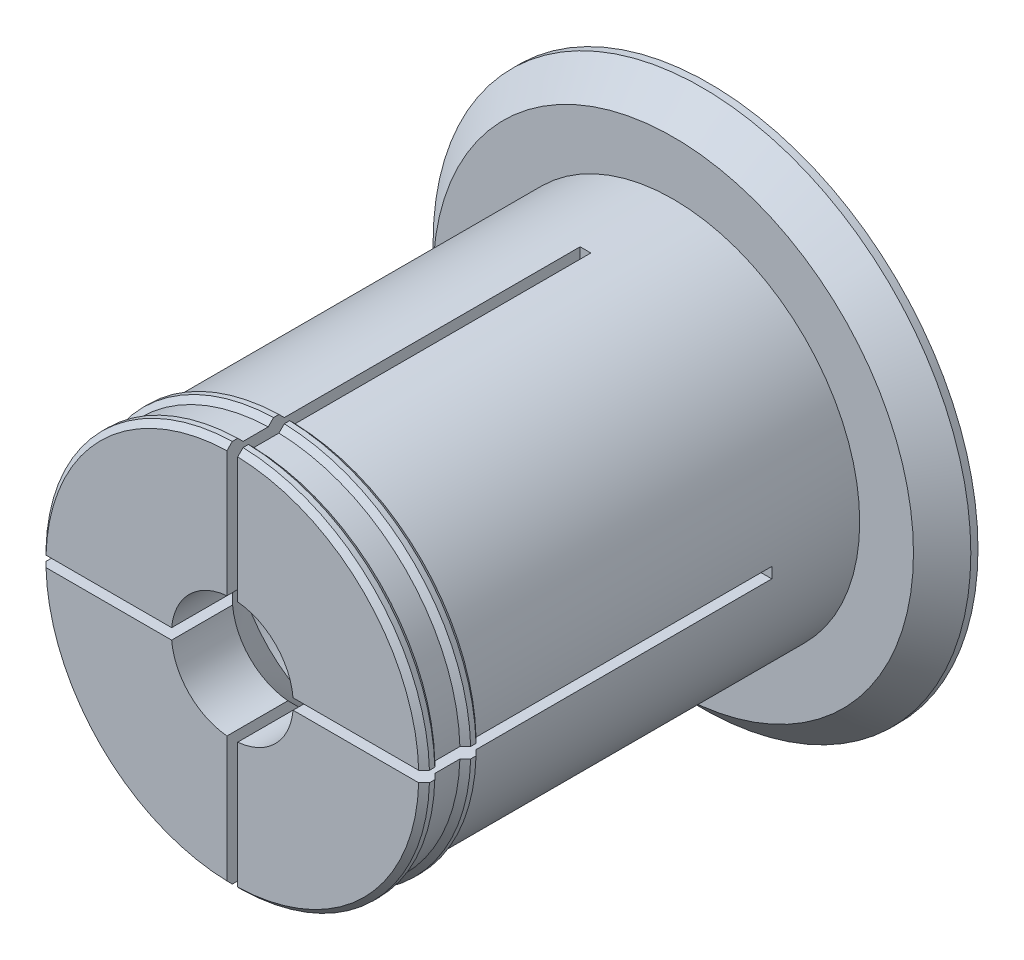
SolidWorks part; units mm, degrees
ref_plane "Front" through (0, 0, 0) normal (0, 0, 1) x (1, 0, 0)
ref_plane "Top" through (0, 0, 0) normal (0, 1, 0) x (1, 0, 0)
ref_plane "Right" through (0, 0, 0) normal (1, 0, 0) x (0, 0, -1)
sketch "Axle base sketch" plane through (0, 0, 0) normal (0, 0, 1) x (1, 0, 0)
  circle A0 centre (0, 0) radius 26
  dimension "D1" = 52
extrude "Axle" add sketch "Axle base sketch" along normal blind 61.5
sketch "Guard base" plane through (0, 0, 0) normal (0, 0, -1) x (-1, 0, 0)
  circle A0 centre (0, 0) radius 37.5
  dimension "D1" = 75
extrude "Guard" add sketch "Guard base" along normal blind 5
sketch "Inner axle hole base" plane through (0, 0, 61.5) normal (0, 0, 1) x (1, 0, 0)
  circle A0 centre (0, 0) radius 8.5
  dimension "D1" = 17
extrude "Inner axle hole" cut sketch "Inner axle hole base" against normal through all
sketch "Mate ring base" plane through (0, 0, 0) normal (0, 1, 0) x (1, 0, 0)
  line L0 (26, -61.5) -> (26.75, -60.75)
  line L1 (26.75, -60.75) -> (26.75, -60)
  line L2 (26.75, -60) -> (26, -59.25)
  line L3 (26.75, -60.75) -> (26.75, -61.5) construction
  line L4 (26.75, -61.5) -> (26, -61.5) construction
  line L5 (26, -59.25) -> (26, -61.5)
  line L6 (26, -61.5) -> (26, 0) construction
  line L8 (26, -55.75) -> (26.75, -55)
  line L9 (26.75, -55) -> (26.75, -54.25)
  line L10 (26.75, -54.25) -> (26, -53.5)
  line L11 (26, -53.5) -> (26, -55.75)
  dimension "D1" = 0.75
  dimension "D2" = 0.75
  dimension "D3" = 5
  dimension "D4" = 0.75
ref_axis "Center Z" through (0, 0, 0) along (0, 0, -1)
revolve "Mate rings" add sketch "Mate ring base" angle 360 about axis through (0, 0, 0) along (0, 0, -1)
sketch "Inner mass remove base" plane through (0, 0, 0) normal (1, 0, 0) x (0, 0, -1)
  line L0 (-61.5, 0) -> (-44.25, -17.25)
  line L1 (-44.25, -17.25) -> (-12.25, -17.25)
  line L2 (-12.25, -17.25) -> (5, 0)
  line L3 (5, 0) -> (-61.5, 0)
  line L4 (5, -8.5) -> (5, 8.5) construction
  line L5 (-44.25, -17.25) -> (-44.25, -8.5) construction
  line L6 (-44.25, -17.25) -> (-44.25, -26) construction
  line L7 (-61.5, 8.5) -> (-61.5, -8.5) construction
  point P9 (-61.5, -8.5)
  point P11 (-61.5, -26)
  dimension "D1" = 135
revolve "Inner mass remove" cut sketch "Inner mass remove base" angle 360 about axis through (0, 0, 0) along (0, 0, -1)
ref_point "Bend room endpoint"
sketch "Bend room base" plane through (0, 0, 61.5) normal (0, 0, 1) x (1, 0, 0)
  line L0 (0.75, -37.5) -> (0.75, 37.5)
  line L1 (0.75, 37.5) -> (-0.75, 37.5)
  line L2 (-0.75, 37.5) -> (-0.75, -37.5)
  line L3 (-0.75, -37.5) -> (0.75, -37.5)
  dimension "D1" = 0.75
  dimension "D2" = 0.75
  dimension "D3" = 37.5
  dimension "D4" = 37.5
extrude "Bend room 1" cut sketch "Bend room base" against normal up to vertex (28.9925 mm away)
pattern_circular "Bend room 2" count 2 every 90 about axis through (0, 0, 0) along (0, 0, -1) of "Bend room 1"
chamfer "Easy removal chamfer" distance 4 angle 45 1 edges at (-37.5, 0, 0)
equation "\"32_92_spool_inner_diameter\"=32"
equation "\"D1@Axle base sketch\"=\"53_55_spool_inner_diameter\"- \"spool_inner_diameter_room\""
equation "\"spool_inner_diameter_room\"=1"
equation "\"32_92_spool_thickness\"=92"
equation "\"D1@Axle\"=\"53_55_spool_thickness\"+\"guard_thickness\"+\"removal_room\"*2"
equation "\"32_92_guard_diameter\"=50"
equation "\"D1@Guard base\"=\"53_55_guard_diameter\""
equation "\"guard_thickness\"=5"
equation "\"D1@Guard\"=\"guard_thickness\""
equation "\"large_inner_axle_diameter\"=20"
equation "\"D1@Inner axle hole base\"=\"small_inner_axle_diameter\""
equation "\"mate_room\"= 0.25"
equation "\"removal_room\"= 0.75"
equation "\"small_inner_axle_diameter\"=17"
equation "\"53_55_spool_inner_diameter\"=53"
equation "\"53_55_spool_thickness\"=55"
equation "\"53_55_guard_diameter\"=75"
equation "\"D1@Mate ring base\"=\"removal_room\""
equation "\"D2@Mate ring base\"=\"removal_room\""
equation "\"D3@Mate ring base\"=\"guard_thickness\""
equation "\"D4@Mate ring base\"=\"removal_room\""
equation "\"D1@Bend room base\" = \"removal_room\""
equation "\"D2@Bend room base\"=\"removal_room\""
equation "\"D3@Bend room base\"=\"53_55_guard_diameter\"/2"
equation "\"D4@Bend room base\"=\"53_55_guard_diameter\"/2"
equation "\"bend_room_length_multiplier\"=3"
equation "\"D1@Easy removal chamfer\"=\"guard_thickness\"-1"
equation "\"32_92_extra_spool_thickness\"=-5"
equation "\"39_92_spool_inner_diameter\"=39"
equation "\"39_92_spool_thickness\"=92"
equation "\"39_92_guard_diameter\"=60"
equation "\"53_55_bend_room_length_multiplier\"=1.5"
